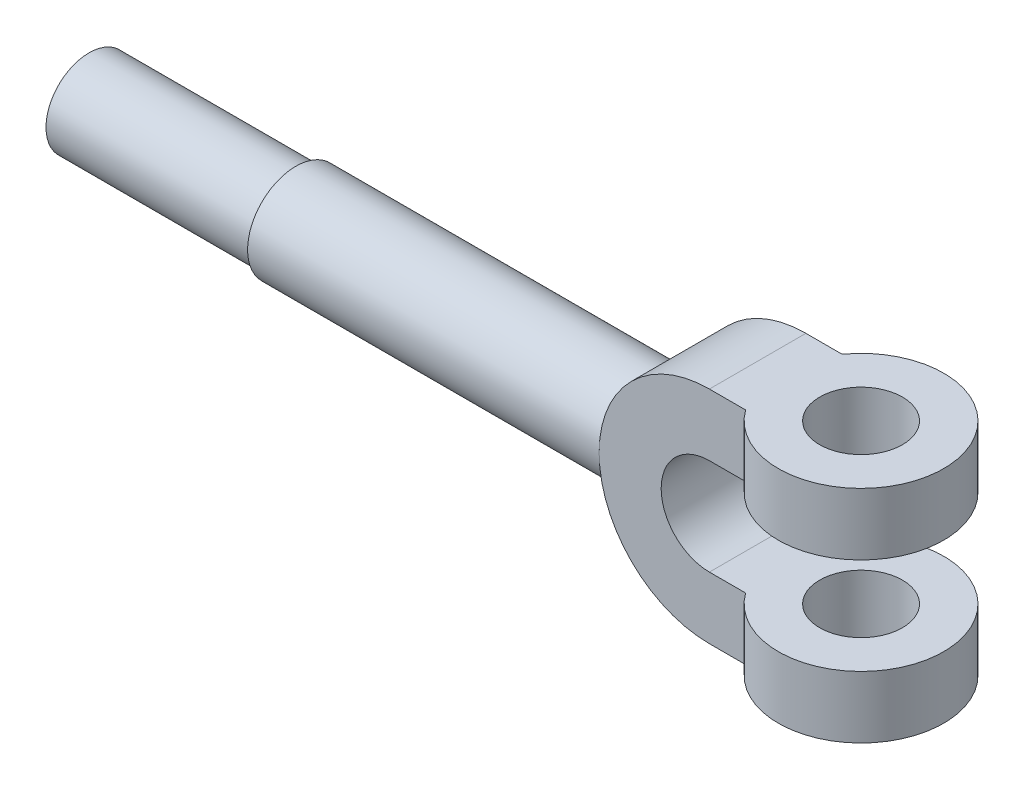
SolidWorks part; units mm, degrees
ref_plane "Front Plane" through (0, 0, 0) normal (0, 0, 1) x (1, 0, 0)
ref_plane "Top Plane" through (0, 0, 0) normal (0, 1, 0) x (1, 0, 0)
ref_plane "Right Plane" through (0, 0, 0) normal (1, 0, 0) x (0, 0, -1)
sketch "Sketch2" plane through (0, 0, 0) normal (0, 0, 1) x (1, 0, 0)
  line L0 (30, 14) -> (30, 32)
  line L1 (-30, 14) -> (30, 14)
  line L3 (-30, -14) -> (30, -14)
  line L5 (-30, 32) -> (30, 32)
  line L7 (-30, -32) -> (30, -32)
  line L9 (30, -14) -> (30, -32)
  arc A0 (-30, 32) -> (-30, -32) centre (-30, 0) ccw
  arc A1 (-30, 14) -> (-30, -14) centre (-30, 0) ccw
  point P4 (0, 0)
  dimension "D7" = 64
  dimension "D8" = 14
  dimension "D1" = 60
  dimension "D2" = 28
  dimension "D3" = 14
  dimension "D4" = 30
  dimension "D5" = 18
  dimension "D6" = 18
  dimension "D9" = 46
extrude "Boss-Extrude1" add sketch "Sketch2" along normal mid plane 28
sketch "Sketch3" plane through (0, 0, 0) normal (1, 0, 0) x (0, 0, -1)
  circle A0 centre (0, 0) radius 14
  dimension "D1" = 28
extrude "Boss-Extrude4" add sketch "Sketch3" against normal blind 104 from offset 60 contours A0 offset against normal yes
sketch "Sketch4" plane through (-164, 0, 0) normal (-1, 0, 0) x (0, 0, 1)
  circle A0 centre (0, 0) radius 12.5
  dimension "D1" = 25
extrude "Boss-Extrude5" add sketch "Sketch4" along normal blind 60 contours A0
sketch "Sketch5" plane through (0, 32, 0) normal (0, 1, 0) x (1, 0, 0)
  circle A0 centre (0, 0) radius 24
  dimension "D1" = 48
extrude "Boss-Extrude7" add sketch "Sketch5" against normal blind 18 contours A0
sketch "Sketch7" plane through (0, -32, 0) normal (0, -1, 0) x (1, 0, 0)
  circle A0 centre (0, 0) radius 24
  dimension "D1" = 48
extrude "Boss-Extrude8" add sketch "Sketch7" against normal blind 18 contours A0
sketch "Sketch8" plane through (0, -32, 0) normal (0, -1, 0) x (1, 0, 0)
  line L6 (-30, -14) -> (-19.4936, -14)
  line L7 (19.4936, -14) -> (30, -14)
  line L8 (30, -14) -> (30, 14)
  line L9 (30, 14) -> (19.4936, 14)
  line L10 (-19.4936, 14) -> (-30, 14)
  line L11 (-30, 14) -> (-30, -14)
  line L13 (19.4936, -14) -> (30, -14)
  line L14 (30, -14) -> (30, 14)
  line L15 (30, 14) -> (19.4936, 14)
  arc A0 (19.4936, -14) -> (19.4936, 14) centre (0, 0) ccw
  arc A2 (-19.4936, -14) -> (19.4936, -14) centre (0, 0) ccw
  arc A3 (19.4936, 14) -> (-19.4936, 14) centre (0, 0) ccw
  dimension "D1" = 0
extrude "Cut-Extrude2" cut sketch "Sketch8" against normal blind 85
ref_plane "Plane1" through (-19.4936, 32, 14) normal (0.5833, 0, 0.8122) x (0.8122, 0, -0.5833)
sketch "Sketch10" plane through (0, -32, 0) normal (0, -1, 0) x (1, 0, 0)
  circle A0 centre (0, 0) radius 12
  dimension "D1" = 24
extrude "Cut-Extrude3" cut sketch "Sketch10" against normal blind 85
